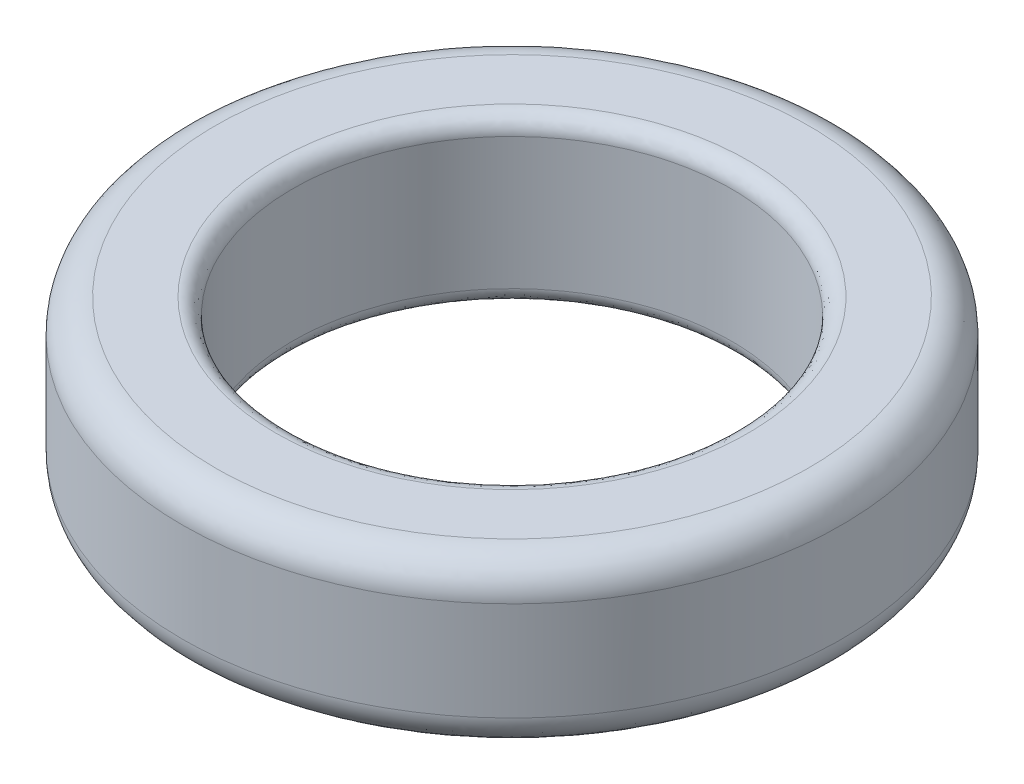
SolidWorks part; units mm, degrees
ref_plane "Front Plane" through (0, 0, 0) normal (0, 0, 1) x (1, 0, 0)
ref_plane "Top Plane" through (0, 0, 0) normal (0, 1, 0) x (1, 0, 0)
ref_plane "Right Plane" through (0, 0, 0) normal (1, 0, 0) x (0, 0, -1)
other "Configuration Table"
sketch "Sketch1" plane through (0, 0, 0) normal (0, 1, 0) x (1, 0, 0)
  circle A0 centre (0, 0) radius 30
  circle A1 centre (0, 0) radius 20
  dimension "D1" = 60
  dimension "D2" = 40
extrude "Boss-Extrude1" add sketch "Sketch1" along normal blind 15
fillet "Fillet1" radius 3 2 edges at (0, 0, 30) (0, 15, 30)
fillet "Fillet2" radius 1.5 2 edges at (0, 0, 20) (0, 15, 20)
